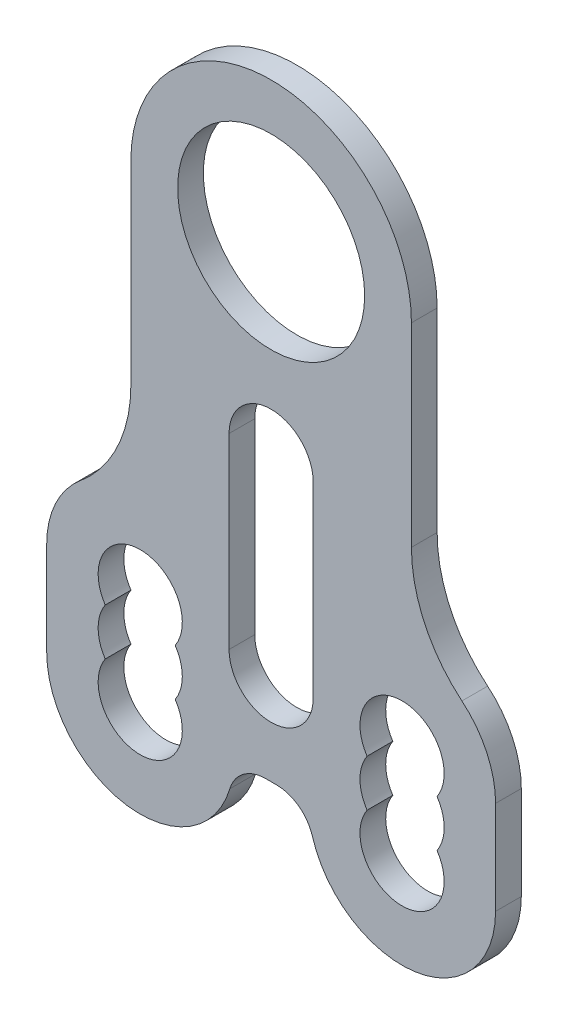
SolidWorks part; units mm, degrees
material "AISI 304"
ref_plane "前视基准面" through (0, 0, 0) normal (0, 0, 1) x (1, 0, 0)
ref_plane "上视基准面" through (0, 0, 0) normal (0, 1, 0) x (1, 0, 0)
ref_plane "右视基准面" through (0, 0, 0) normal (1, 0, 0) x (0, 0, -1)
sketch "草图1" plane through (0, 0, 0) normal (0, 0, 1) x (1, 0, 0)
  line L0 (0, 0) -> (0, -60) construction
  line L1 (14, -60) -> (-14, -60) construction
  line L2 (-14, -60) -> (-14, -50) construction
  line L3 (-14, -50) -> (-14, -40) construction
  line L4 (-24, -40) -> (-24, -50)
  line L6 (-15, 0) -> (-15, -20.7906)
  line L7 (-0.5836, -50) -> (0.5836, -50)
  line L8 (15, 0) -> (15, -20.7906)
  line L9 (14, -50) -> (14, -40) construction
  line L10 (14, -60) -> (14, -50) construction
  line L11 (24, -40) -> (24, -50)
  line L12 (0, -40) -> (0, -20) construction
  line L13 (-4.5, -20) -> (-4.5, -40)
  line L14 (4.5, -20) -> (4.5, -40)
  circle A0 centre (0, 0) radius 10
  arc A1 (15, 0) -> (-15, 0) centre (0, 0) ccw
  arc A2 (-24, -50) -> (-4.4169, -52.8571) centre (-14, -50) ccw
  arc A3 (-17.7417, -47.5) -> (-10.2583, -47.5) centre (-14, -50) ccw
  arc A4 (-10.2583, -42.5) -> (-17.7417, -42.5) centre (-14, -40) ccw
  arc A5 (-17.7417, -42.5) -> (-17.7417, -47.5) centre (-14, -45) ccw
  arc A6 (-10.2583, -47.5) -> (-10.2583, -42.5) centre (-14, -45) ccw
  arc A7 (-20.4, -32.3163) -> (-24, -40) centre (-14, -40) ccw
  arc A8 (-20.4, -32.3163) -> (-15, -20.7906) centre (-30, -20.7906) ccw
  arc A9 (20.4, -32.3163) -> (15, -20.7906) centre (30, -20.7906) cw
  arc A10 (20.4, -32.3163) -> (24, -40) centre (14, -40) cw
  arc A11 (10.2583, -47.5) -> (10.2583, -42.5) centre (14, -45) cw
  arc A12 (17.7417, -42.5) -> (17.7417, -47.5) centre (14, -45) cw
  arc A13 (10.2583, -42.5) -> (17.7417, -42.5) centre (14, -40) cw
  arc A14 (17.7417, -47.5) -> (10.2583, -47.5) centre (14, -50) cw
  arc A15 (24, -50) -> (4.4169, -52.8571) centre (14, -50) cw
  arc A16 (4.4169, -52.8571) -> (0.5836, -50) centre (0.5836, -54) ccw
  arc A17 (-4.4169, -52.8571) -> (-0.5836, -50) centre (-0.5836, -54) cw
  arc A18 (-4.5, -40) -> (4.5, -40) centre (0, -40) ccw
  arc A19 (4.5, -20) -> (-4.5, -20) centre (0, -20) ccw
  point P36 (0, -50)
  point P37 (4, -50)
  point P40 (-4, -50)
  dimension "D1" = 15
  dimension "D2" = 4
extrude "凸台-拉伸1" add sketch "草图1" along normal blind 2.75
